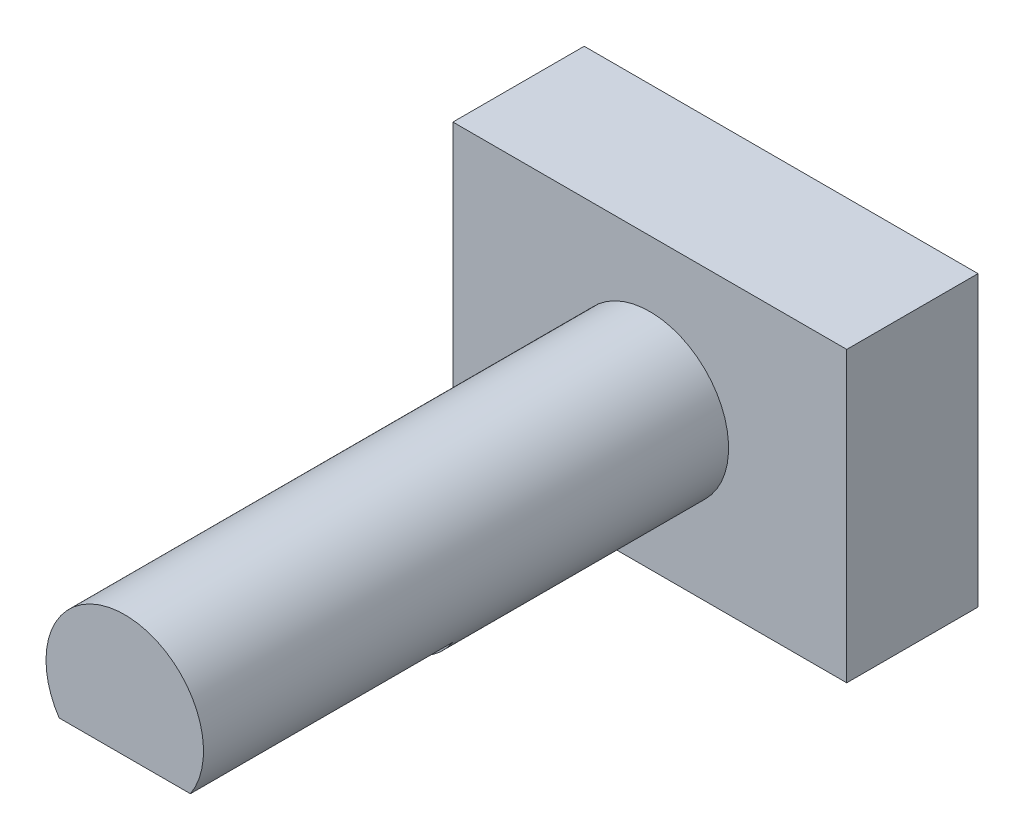
SolidWorks part; units mm, degrees
ref_plane "Plan de face" through (0, 0, 0) normal (0, 0, 1) x (1, 0, 0)
ref_plane "Plan de dessus" through (0, 0, 0) normal (0, 1, 0) x (1, 0, 0)
ref_plane "Plan de droite" through (0, 0, 0) normal (1, 0, 0) x (0, 0, -1)
sketch "Esquisse1" plane through (0, 0, 0) normal (0, 0, 1) x (1, 0, 0)
  line L1 (-7.5, -5.5) -> (7.5, -5.5)
  line L2 (-7.5, -5.5) -> (-7.5, 5.5)
  line L3 (-7.5, 5.5) -> (7.5, 5.5)
  line L4 (7.5, -5.5) -> (7.5, 5.5)
  dimension "D1" = 11
  dimension "D2" = 15
  dimension "D3" = 5.5
  dimension "D4" = 7.5
extrude "Boss.-Extru.1" add sketch "Esquisse1" along normal blind 5
sketch "Esquisse2" plane through (0, 0, 5) normal (0, 0, 1) x (1, 0, 0)
  circle A0 centre (0, 0) radius 3
  dimension "D1" = 6
extrude "Boss.-Extru.2" add sketch "Esquisse2" along normal blind 20
sketch "Esquisse3" plane through (0, 0, 25) normal (0, 0, 1) x (1, 0, 0)
  line L0 (-2.5, -1.6583) -> (2.5, -1.6583)
  circle A0 centre (0, 0) radius 3 construction
  circle A1 centre (0, 0) radius 3 construction
  arc A2 (-2.5, -1.6583) -> (2.5, -1.6583) centre (0, 0) ccw
  dimension "D1" = 5
extrude "Enlèv. mat.-Extru.1" cut sketch "Esquisse3" against normal blind 10
